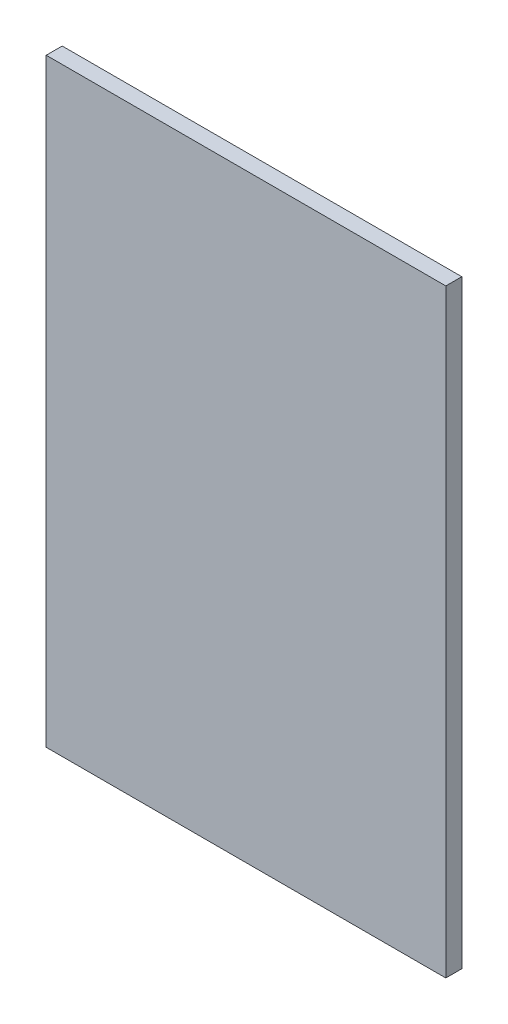
SolidWorks part; units mm, degrees
material "Cardboard"
ref_plane "Front Plane" through (0, 0, 0) normal (0, 0, 1) x (1, 0, 0)
ref_plane "Top Plane" through (0, 0, 0) normal (0, 1, 0) x (1, 0, 0)
ref_plane "Right Plane" through (0, 0, 0) normal (1, 0, 0) x (0, 0, -1)
sketch "Sketch1" plane through (0, 0, 0) normal (0, 0, 1) x (1, 0, 0)
  line L1 (0, 0) -> (100, 0)
  line L2 (0, 0) -> (0, 150)
  line L3 (0, 150) -> (100, 150)
  line L4 (100, 0) -> (100, 150)
  dimension "D1" = 150
  dimension "D2" = 100
extrude "Boss-Extrude1" add sketch "Sketch1" along normal blind 4
